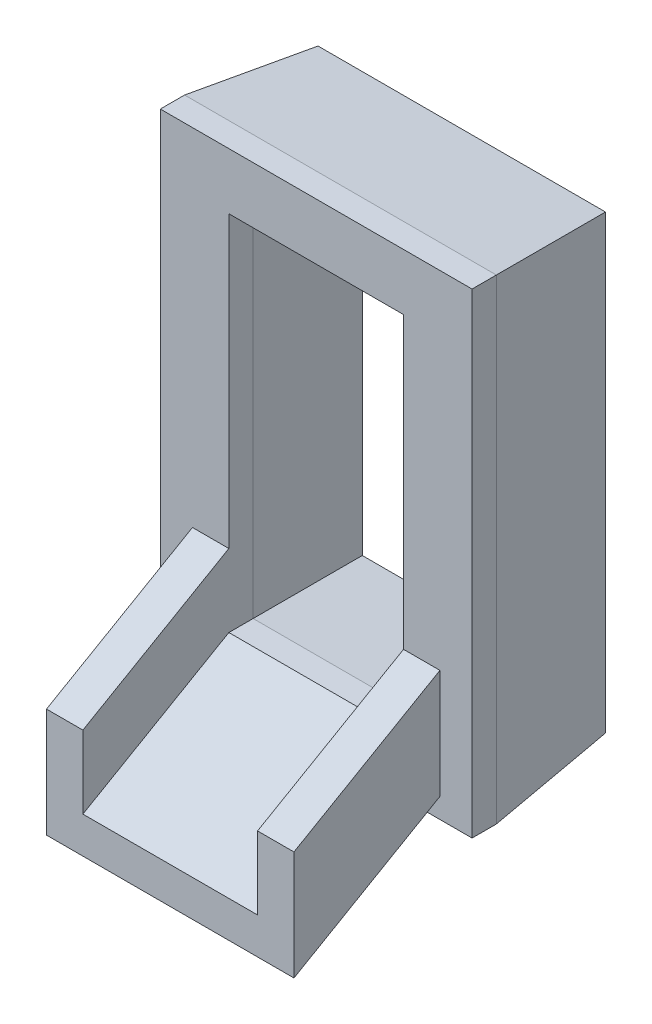
SolidWorks part; units mm, degrees
ref_plane "Front Plane" through (0, 0, 0) normal (0, 0, 1) x (1, 0, 0)
ref_plane "Top Plane" through (0, 0, 0) normal (0, 1, 0) x (1, 0, 0)
ref_plane "Right Plane" through (0, 0, 0) normal (1, 0, 0) x (0, 0, -1)
sketch "Sketch3" plane through (0, 0, 0) normal (0, 0, 1) x (1, 0, 0)
  line L1 (0, 0) -> (25.7, 0)
  line L2 (0, 0) -> (0, 39.2)
  line L3 (0, 39.2) -> (25.7, 39.2)
  line L4 (25.7, 0) -> (25.7, 39.2)
  line L5 (5.65, 4.65) -> (20.05, 4.65)
  line L6 (5.65, 4.65) -> (5.65, 34.55)
  line L7 (5.65, 34.55) -> (20.05, 34.55)
  line L8 (20.05, 4.65) -> (20.05, 34.55)
  point P9 (12.85, 34.55)
  point P10 (12.85, 39.2)
  point P11 (5.65, 19.6)
  point P12 (0, 19.6)
  dimension "D1" = 25.7
  dimension "D2" = 39.2
  dimension "D3" = 14.4
  dimension "D4" = 29.9
extrude "Boss-Extrude2" add sketch "Sketch3" along normal blind 12
chamfer "Chamfer1" distance 1 distance2 10 8 edges at (25.7, 19.6, 0) (12.85, 39.2, 0) (0, 19.6, 0) (12.85, 0, 0) (12.85, 4.65, 0) (20.05, 19.6, 0) (12.85, 34.55, 0) (5.65, 19.6, 0)
sketch "Sketch4" plane through (0, 0, 12) normal (0, 0, 1) x (1, 0, 0)
  line L0 (5.65, 10.65) -> (2.65, 10.65)
  line L1 (5.65, 34.55) -> (5.65, 4.65) construction
  line L2 (2.65, 10.65) -> (2.65, 1.65)
  line L3 (2.65, 1.65) -> (23.05, 1.65)
  line L4 (23.05, 1.65) -> (23.05, 10.65)
  line L5 (23.05, 10.65) -> (20.05, 10.65)
  line L6 (20.05, 4.65) -> (20.05, 34.55) construction
  line L7 (20.05, 10.65) -> (20.05, 4.65)
  line L8 (20.05, 4.65) -> (5.65, 4.65)
  line L9 (5.65, 4.65) -> (5.65, 10.65)
  dimension "D1" = 3
  dimension "D2" = 3
  dimension "D3" = 3
  dimension "D4" = 6
ref_plane "Plane1" through (12.85, 0, 0) normal (-1, 0, 0) x (0, 0, 1)
sketch "Sketch6" plane through (12.85, 0, 0) normal (-1, 0, 0) x (0, 0, 1)
  line L0 (12, 4.65) -> (24.0333, -2.2974)
  line L2 (12, 10.65) -> (12, 1.65) construction
  dimension "D1" = 60
sweep "Sweep1" add profiles "Sketch4" path "Sketch6"
